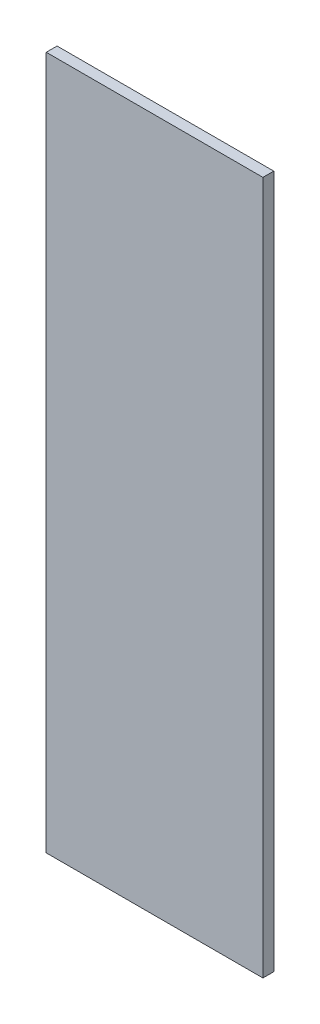
SolidWorks part; units mm, degrees
ref_plane "Front Plane" through (0, 0, 0) normal (0, 0, 1) x (1, 0, 0)
ref_plane "Top Plane" through (0, 0, 0) normal (0, 1, 0) x (1, 0, 0)
ref_plane "Right Plane" through (0, 0, 0) normal (1, 0, 0) x (0, 0, -1)
sketch "Sketch1" plane through (0, 0, 0) normal (0, 0, 1) x (1, 0, 0)
  line L1 (-50, -160) -> (50, -160)
  line L2 (-50, -160) -> (-50, 160)
  line L3 (-50, 160) -> (50, 160)
  line L4 (50, -160) -> (50, 160)
  line L5 (-50, -160) -> (50, 160) construction
  line L6 (-50, 160) -> (50, -160) construction
  point P0 (0, 0)
  dimension "D1" = 320
  dimension "D2" = 100
extrude "Boss-Extrude1" add sketch "Sketch1" along normal blind 5
